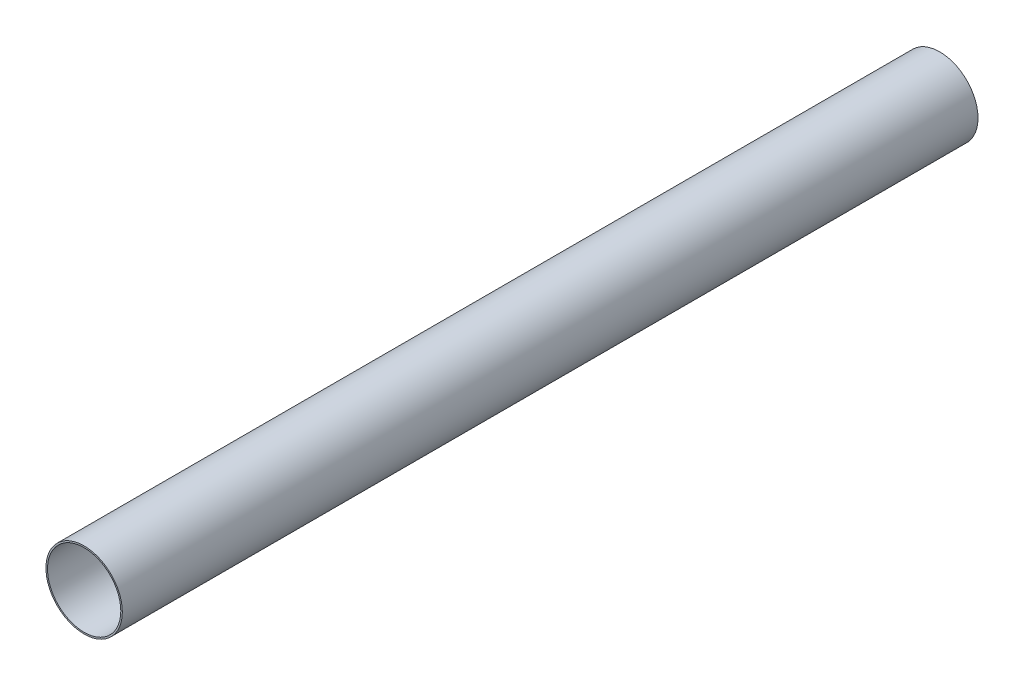
SolidWorks part; units mm, degrees
material "Thornel Mat VMA"
ref_plane "Front Plane" through (0, 0, 0) normal (0, 0, 1) x (1, 0, 0)
ref_plane "Top Plane" through (0, 0, 0) normal (0, 1, 0) x (1, 0, 0)
ref_plane "Right Plane" through (0, 0, 0) normal (1, 0, 0) x (0, 0, -1)
sketch "Sketch1" plane through (0, 0, 0) normal (0, 0, 1) x (1, 0, 0)
  circle A0 centre (0, 0) radius 76.2
  circle A1 centre (0, 0) radius 79.375
  dimension "D1" = 152.4
  dimension "D2" = 3.175
extrude "Boss-Extrude1" add sketch "Sketch1" along normal blind 1778
